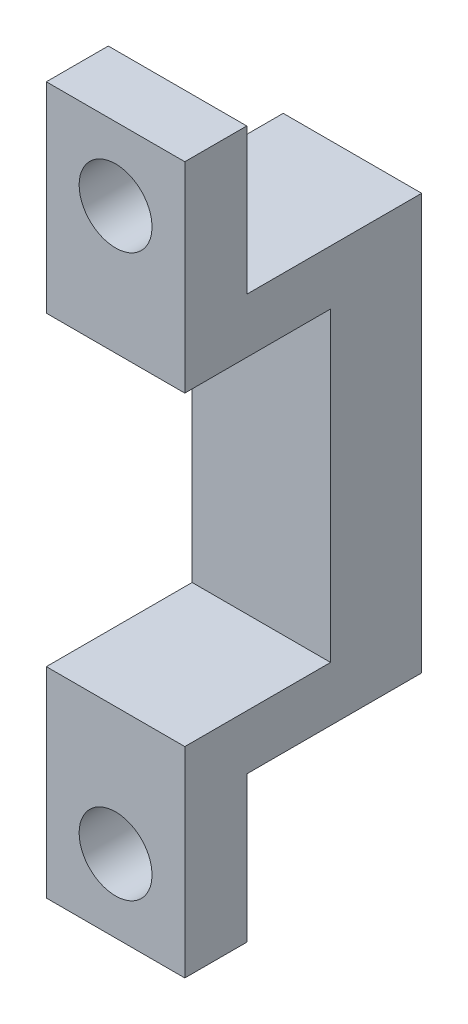
SolidWorks part; units mm, degrees
ref_plane "Front Plane" through (0, 0, 0) normal (0, 0, 1) x (1, 0, 0)
ref_plane "Top Plane" through (0, 0, 0) normal (0, 1, 0) x (1, 0, 0)
ref_plane "Right Plane" through (0, 0, 0) normal (1, 0, 0) x (0, 0, -1)
sketch "Sketch1" plane through (0, 0, 0) normal (0, 0, 1) x (1, 0, 0)
  line L0 (-9.5, -28.5) -> (-9.5, 28.5)
  line L1 (-9.5, 28.5) -> (9.5, 28.5)
  line L2 (9.5, 28.5) -> (9.5, -28.5)
  line L3 (9.5, -28.5) -> (-9.5, -28.5)
  dimension "D1" = 19
  dimension "D2" = 57
  dimension "D3" = 28.5
  dimension "D4" = 9.5
extrude "Boss-Extrude1" add sketch "Sketch1" along normal blind 12.5
sketch "Sketch2" plane through (0, 0, 12.5) normal (0, 0, 1) x (1, 0, 0)
  line L0 (-9.5, -21) -> (9.5, -21)
  line L1 (-9.5, 28.5) -> (-9.5, -28.5) construction
  line L2 (9.5, -28.5) -> (9.5, 28.5) construction
  line L3 (9.5, -21) -> (9.5, -28.5)
  line L4 (9.5, -28.5) -> (-9.5, -28.5)
  line L5 (-9.5, -28.5) -> (-9.5, -21)
  line L6 (-9.5, 28.5) -> (9.5, 28.5)
  line L7 (9.5, 28.5) -> (9.5, 21)
  line L8 (9.5, 21) -> (-9.5, 21)
  line L9 (-9.5, 21) -> (-9.5, 28.5)
  line L10 (9.5, 28.5) -> (-9.5, 28.5) construction
  dimension "D1" = 7.5
  dimension "D2" = 7.5
  dimension "D3" = 0
  dimension "D4" = 0
  dimension "D5" = 0
extrude "Boss-Extrude2" add sketch "Sketch2" along normal blind 20
sketch "Sketch3" plane through (0, -28.5, 0) normal (0, -1, 0) x (1, 0, 0)
  line L0 (-9.5, 24) -> (9.5, 24)
  line L1 (-9.5, 32.5) -> (-9.5, 0) construction
  line L2 (9.5, 32.5) -> (9.5, 0) construction
  line L3 (9.5, 24) -> (9.5, 32.5)
  line L4 (9.5, 32.5) -> (-9.5, 32.5)
  line L5 (-9.5, 32.5) -> (-9.5, 24)
  dimension "D1" = 8.5
extrude "Boss-Extrude3" add sketch "Sketch3" along normal blind 20
sketch "Sketch4" plane through (0, 28.5, 0) normal (0, 1, 0) x (1, 0, 0)
  line L0 (-9.5, -24) -> (9.5, -24)
  line L1 (-9.5, -32.5) -> (-9.5, 0) construction
  line L2 (9.5, -32.5) -> (9.5, 0) construction
  line L3 (9.5, -24) -> (9.5, -32.5)
  line L4 (9.5, -32.5) -> (-9.5, -32.5)
  line L5 (-9.5, -32.5) -> (-9.5, -24)
  dimension "D1" = 8.5
extrude "Boss-Extrude4" add sketch "Sketch4" along normal blind 20
sketch "Sketch5" plane through (0, 0, 24) normal (0, 0, -1) x (-1, 0, 0)
  line L1 (-9.5, 28.5) -> (9.5, 28.5) construction
  line L2 (9.5, -48.5) -> (-9.5, -48.5) construction
  circle A0 centre (0, 38.5) radius 5
  circle A1 centre (0, -38.5) radius 5
  dimension "D1" = 10
  dimension "D2" = 10
  dimension "D3" = 0
  dimension "D4" = 10
extrude "Cut-Extrude1" cut sketch "Sketch5" against normal blind 20
